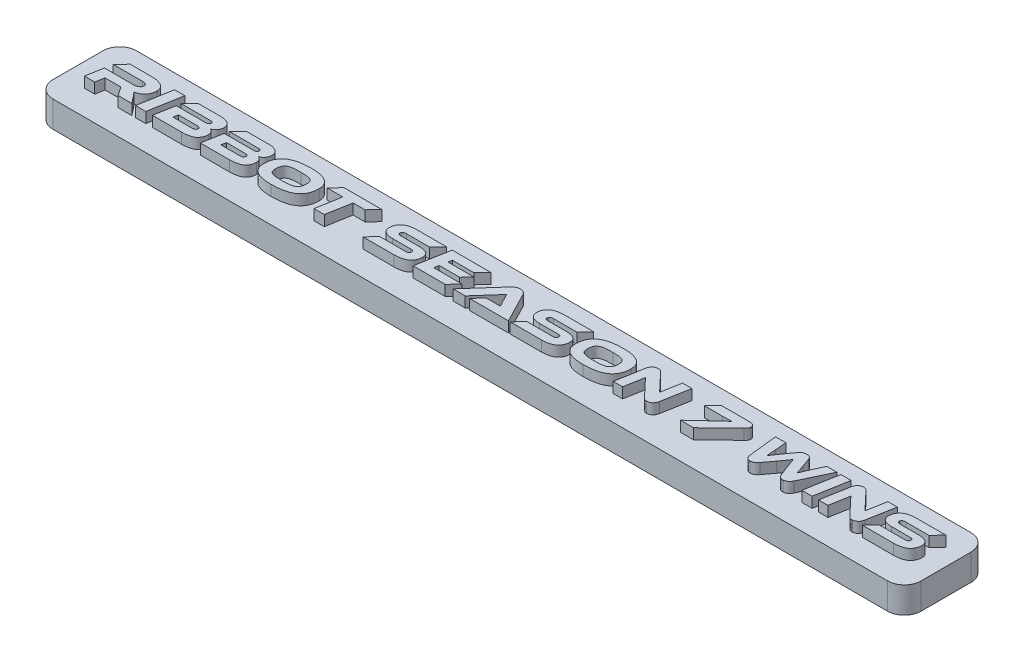
SolidWorks part; units mm, degrees
ref_plane "Front Plane" through (0, 0, 0) normal (0, 0, 1) x (1, 0, 0)
ref_plane "Top Plane" through (0, 0, 0) normal (0, 1, 0) x (1, 0, 0)
ref_plane "Right Plane" through (0, 0, 0) normal (1, 0, 0) x (0, 0, -1)
sketch "Sketch1" plane through (0, 0, 0) normal (0, 1, 0) x (1, 0, 0)
  line L0 (-82.55, -3.175) -> (82.55, -3.175) construction
  line L1 (-82.55, -7.9375) -> (82.55, -7.9375)
  line L2 (-82.55, -7.9375) -> (-82.55, 7.9375)
  line L3 (-82.55, 7.9375) -> (82.55, 7.9375)
  line L4 (82.55, -7.9375) -> (82.55, 7.9375)
  line L5 (-82.55, -7.9375) -> (82.55, 7.9375) construction
  line L6 (-82.55, 7.9375) -> (82.55, -7.9375) construction
  point P0 (0, 0)
  dimension "D1" = 165.1
  dimension "D2" = 15.875
  dimension "D3" = 4.7625
extrude "Boss-Extrude1" add sketch "Sketch1" against normal blind 5
fillet "Fillet1" radius 3.175 4 edges at (82.55, -2.5, -7.9375) (-82.55, -2.5, 7.9375) (82.55, -2.5, 7.9375) (-82.55, -2.5, -7.9375)
sketch "Sketch2" plane through (0, 0, 0) normal (0, 1, 0) x (1, 0, 0)
  line L0 (-82.55, -3.175) -> (82.55, -3.175) construction
  line L1 (82.55, -4.7625) -> (82.55, 4.7625) construction
  line L2 (-82.55, 4.7625) -> (-82.55, -4.7625) construction
  text T0 "Ribbot Season 7 Wins" font "Ethnocentric Rg" height in points 24
  dimension "D1" = 3.175
extrude "Boss-Extrude2" add sketch "Sketch2" along normal blind 2
sketch "Sketch3" plane through (0, -5, 0) normal (0, -1, 0) x (1, 0, 0)
  line L0 (-77.7875, 0) -> (0, 0) construction
  line L1 (0, 0) -> (77.7875, 0) construction
  line L2 (-82.55, -4.7625) -> (-82.55, 4.7625) construction
  circle A0 centre (-77.7875, 0) radius 0.9
  circle A1 centre (0, 0) radius 0.9
  circle A2 centre (77.7875, 0) radius 0.9
  dimension "D2" = 1.8
  dimension "D1" = 4.7625
extrude "Cut-Extrude1" cut sketch "Sketch3" against normal blind 4
